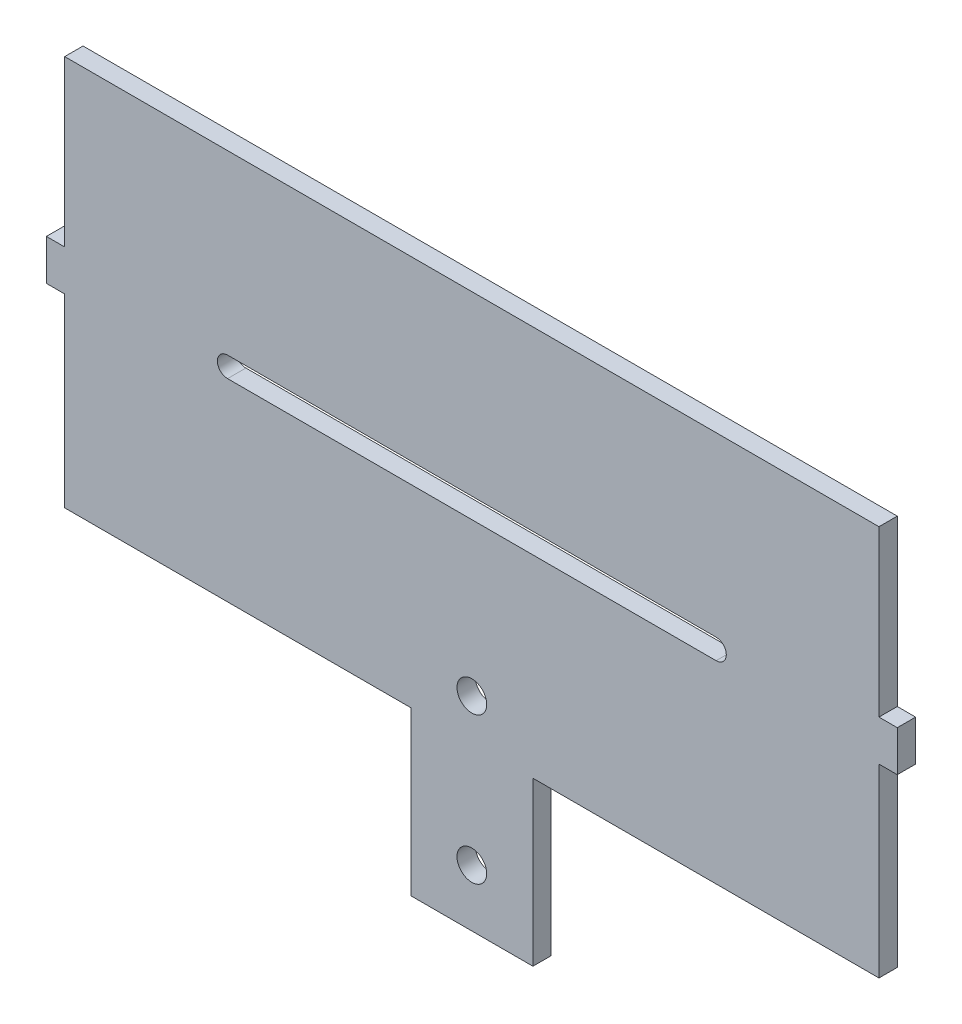
SolidWorks part; units mm, degrees
ref_plane "Front Plane" through (0, 0, 0) normal (0, 0, 1) x (1, 0, 0)
ref_plane "Top Plane" through (0, 0, 0) normal (0, 1, 0) x (1, 0, 0)
ref_plane "Right Plane" through (0, 0, 0) normal (1, 0, 0) x (0, 0, -1)
sketch "Sketch1" plane through (0, 0, 0) normal (0, 0, 1) x (1, 0, 0)
  line L0 (19.05, -63.5) -> (127, -63.5)
  line L1 (-127, -63.5) -> (-19.05, -63.5)
  line L2 (-127, -63.5) -> (-127, -5.715)
  line L3 (-127, 63.5) -> (127, 63.5)
  line L4 (127, -63.5) -> (127, -5.715)
  line L5 (-127, -63.5) -> (127, 63.5) construction
  line L6 (-127, 63.5) -> (127, -63.5) construction
  line L11 (-127, 6.985) -> (-127, 63.5)
  line L12 (-132.715, -5.715) -> (-127, -5.715)
  line L13 (-132.715, -5.715) -> (-132.715, 6.985)
  line L14 (-132.715, 6.985) -> (-127, 6.985)
  line L16 (0, -55) -> (0, 55) construction
  line L17 (132.715, -5.715) -> (127, -5.715)
  line L18 (132.715, -5.715) -> (132.715, 6.985)
  line L19 (132.715, 6.985) -> (127, 6.985)
  line L20 (127, 6.985) -> (127, 63.5)
  line L22 (-19.05, -114.3) -> (19.05, -114.3)
  line L23 (-19.05, -114.3) -> (-19.05, -63.5)
  line L25 (19.05, -114.3) -> (19.05, -63.5)
  point P0 (0, 0)
  point P6 (0, -63.5)
  point P9 (0, -63.5)
  point P10 (-127, 0)
  dimension "D1" = 127
  dimension "D2" = 254
  dimension "D3" = 38.1
  dimension "D4" = 50.8
  dimension "D5" = 12.7
  dimension "D6" = 57.785
extrude "Boss-Extrude1" add sketch "Sketch1" along normal blind 5.715
sketch "Sketch2" plane through (0, 0, 5.715) normal (0, 0, 1) x (1, 0, 0)
  line L0 (76.2, 0) -> (-76.2, 0) construction
  line L1 (76.2, -3.175) -> (-76.2, -3.175)
  line L2 (76.2, 3.175) -> (-76.2, 3.175)
  arc A0 (76.2, -3.175) -> (76.2, 3.175) centre (76.2, 0) ccw
  arc A1 (-76.2, 3.175) -> (-76.2, -3.175) centre (-76.2, 0) ccw
  point P3 (0, 0)
  dimension "D1" = 152.4
  dimension "D2" = 6.35
extrude "Cut-Extrude1" cut sketch "Sketch2" against normal through all
sketch "Sketch4" plane through (0, 0, 5.715) normal (0, 0, 1) x (1, 0, 0)
  line L0 (19.05, -63.5) -> (127, -63.5) construction
  circle A0 centre (0, -50.8) radius 4.6355
  dimension "D1" = 9.271
  dimension "D2" = 12.7
extrude "Cut-Extrude2" cut sketch "Sketch4" against normal through all both
sketch "Sketch5" plane through (0, 0, 5.715) normal (0, 0, 1) x (1, 0, 0)
  line L0 (-127, 58.42) -> (127, 58.42)
  line L1 (-127, 63.5) -> (-127, 6.985) construction
  line L2 (127, 6.985) -> (127, 63.5) construction
  line L3 (127, 63.5) -> (-127, 63.5) construction
  line L4 (-127, 58.42) -> (-127, 63.5)
  line L5 (-127, 63.5) -> (127, 63.5)
  line L6 (127, 63.5) -> (127, 58.42)
  dimension "D1" = 5.08
extrude "Cut-Extrude3" cut sketch "Sketch5" against normal through all
sketch "Sketch6" plane through (0, 0, 5.715) normal (0, 0, 1) x (1, 0, 0)
  line L1 (-127, -63.5) -> (-19.05, -63.5) construction
  circle A0 centre (0, -96.52) radius 4.6355
  dimension "D1" = 9.271
  dimension "D3" = 33.02
extrude "Cut-Extrude4" cut sketch "Sketch6" against normal through all
